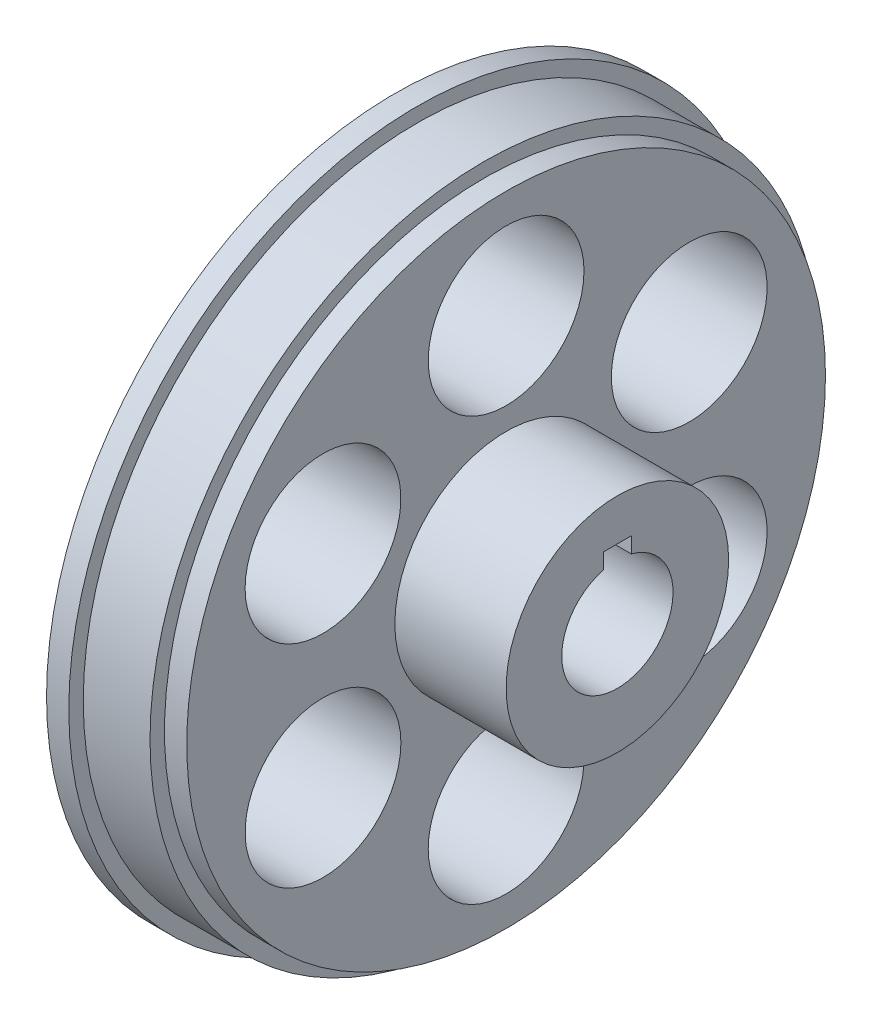
SolidWorks part; units mm, degrees
material "Plain Carbon Steel"
ref_plane "Front Plane" through (0, 0, 0) normal (0, 0, 1) x (1, 0, 0)
ref_plane "Top Plane" through (0, 0, 0) normal (0, 1, 0) x (1, 0, 0)
ref_plane "Right Plane" through (0, 0, 0) normal (1, 0, 0) x (0, 0, -1)
sketch "Sketch1" plane through (0, 0, 0) normal (1, 0, 0) x (0, 0, -1)
  line L0 (0, 7.9375) -> (0, 4.7625) construction
  line L1 (-1.5875, 7.9375) -> (1.5875, 7.9375)
  line L2 (-1.5875, 7.9375) -> (-1.5875, 4.7625)
  line L3 (-1.5875, 4.7625) -> (1.5875, 4.7625)
  line L4 (1.5875, 7.9375) -> (1.5875, 4.7625)
  line L5 (0, 4.7625) -> (1.5875, 6.35) construction
  line L6 (1.5875, 6.35) -> (-1.5875, 6.35) construction
  line L7 (0, 4.7625) -> (0, 0) construction
  circle A0 centre (0, 0) radius 6.35
  circle A1 centre (0, 0) radius 25.4
  dimension "D1" = 6.35
  dimension "D2" = 1.5875
  dimension "D3" = 3.175
extrude "Boss-Extrude1" add sketch "Sketch1" along normal blind 25.4 contours A1 A0 L2 L1 L4
sketch "Sketch2" plane through (0, 0, 0) normal (-1, 0, 0) x (0, 0, 1)
  circle A0 centre (0, 0) radius 10.9141
  circle A1 centre (0, 0) radius 38.1
extrude "Boss-Extrude2" add sketch "Sketch2" against normal blind 12.7
sketch "Sketch3" plane through (25.4, 0, 0) normal (1, 0, 0) x (0, 0, -1)
  circle A0 centre (0, 0) radius 12.7
  circle A1 centre (0, 0) radius 25.4
extrude "Cut-Extrude1" cut sketch "Sketch3" against normal up to surface (12.7 mm away) up to face at (12.7, 0, 38.1)
sketch "Sketch4" plane through (12.7, 0, 0) normal (1, 0, 0) x (0, 0, -1)
  line L0 (0, 12.7) -> (0, 35.56) construction
  circle A0 centre (0, 0) radius 12.7 construction
  circle A1 centre (0, 0) radius 12.7 construction
  circle A2 centre (0, 24.13) radius 8.89
extrude "Cut-Extrude2" cut sketch "Sketch4" against normal through all
pattern_circular "CirPattern1" count 6 over 360 about axis through (0, 0, 0) along (1, 0, 0) of "Cut-Extrude2"
sketch "Sketch5" plane through (0, 0, 0) normal (-1, 0, 0) x (0, 0, 1)
  circle A0 centre (0, 0) radius 39.751
  circle A1 centre (0, 0) radius 38.1
extrude "Boss-Extrude3" add sketch "Sketch5" against normal blind 2.54
sketch "Sketch6" plane through (12.7, 0, 0) normal (1, 0, 0) x (0, 0, -1)
  circle A0 centre (0, 0) radius 36.449
  circle A1 centre (0, 0) radius 38.1
extrude "Cut-Extrude3" cut sketch "Sketch6" against normal blind 2.54
